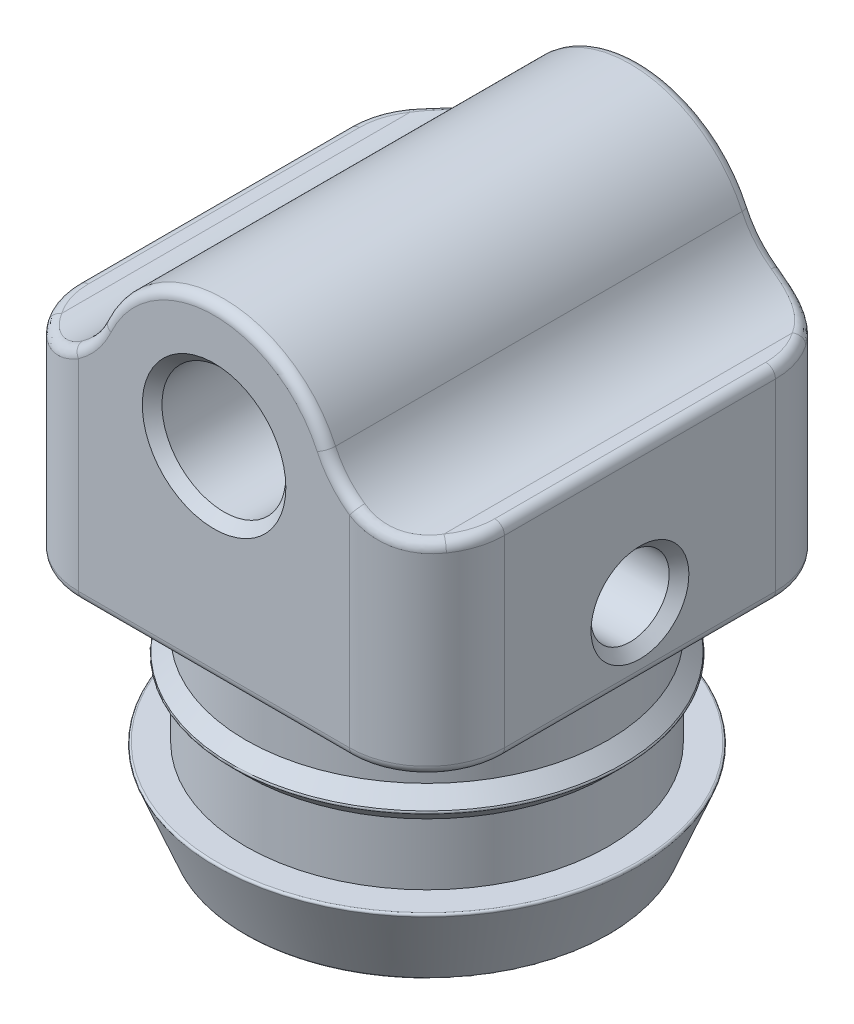
SolidWorks part; units mm, degrees
ref_plane "Front Plane" through (0, 0, 0) normal (0, 0, 1) x (1, 0, 0)
ref_plane "Top Plane" through (0, 0, 0) normal (0, 1, 0) x (1, 0, 0)
ref_plane "Right Plane" through (0, 0, 0) normal (1, 0, 0) x (0, 0, -1)
sketch "Sketch1" plane through (0, 0, 0) normal (0, 0, 1) x (1, 0, 0)
  line L3 (0, 0) -> (0, -10.5) construction
  line L4 (-11, 0) -> (-6.35, 0)
  line L5 (-11, 0) -> (-11, -10.5)
  line L6 (-11, -10.5) -> (11, -10.5)
  line L7 (11, 0) -> (11, -10.5)
  line L8 (6.35, 0) -> (11, 0)
  circle A0 centre (0, 0) radius 3.2
  arc A1 (6.35, 0) -> (-6.35, 0) centre (0, 0) ccw
  dimension "D1" = 6.4
  dimension "D2" = 12.7
  dimension "D4" = 22
  dimension "D5" = 10.5
extrude "Boss-Extrude1" add sketch "Sketch1" along normal mid plane 22
sketch3d "3DSketch1" plane through (0, 0, 0) normal (0, 0, 1) x (1, 0, 0)
  dimension "D1" = 12.7
sketch "Sketch2" plane through (0, 0, 0) normal (0, 0, 1) x (1, 0, 0)
  line L0 (0, 9.544) -> (0, -9.544) construction
  line L1 (0, -10) -> (9.365, -10)
  line L4 (0, -22.7) -> (9.365, -22.7)
  line L10 (0, -22.7) -> (0, -10)
  line L11 (9.365, -22.7) -> (10.9525, -18.7312)
  line L12 (10.9525, -18.7312) -> (9.365, -18.7312)
  line L13 (9.365, -18.7312) -> (9.365, -15.5562)
  line L14 (9.365, -15.5562) -> (10.1587, -14.7625)
  line L15 (10.1587, -14.7625) -> (9.365, -13.9687)
  line L16 (10.1587, -14.7625) -> (9.365, -14.7625) construction
  line L17 (9.365, -13.9687) -> (9.365, -10)
  dimension "D1" = 18.73
  dimension "D2" = 12.7
  dimension "D3" = 1.5875
  dimension "D4" = 3.9688
  dimension "D5" = 0.7937
  dimension "D6" = 7.9375
  dimension "D7" = 10
revolve "Revolve1" add sketch "Sketch2" angle 360 about L0
sketch "Sketch3" plane through (0, -22.7, 0) normal (0, -1, 0) x (1, 0, 0)
  circle A0 centre (0, 0) radius 2.3813
  dimension "D1" = 4.7625
extrude "Cut-Extrude1" cut sketch "Sketch3" against normal blind 18 contours A0
hole_wizard "#10-32 Tapped Hole1" positions "Sketch4" profile "Sketch5" tap size "#10-32" standard "ANSI Inch"
sketch "Sketch4" plane through (11, 0, 0) normal (1, 0, 0) x (0, 0, -1)
  point P0 (0, -7)
  dimension "D1" = 7
sketch "Sketch5" plane through (11, -7, 0) normal (0, 1, 0) x (0, 0, -1)
  line L0 (0, 0) -> (0, 8.6188)
  line L1 (0, 8.6188) -> (2.0193, 8.6188)
  line L2 (2.0193, 8.6188) -> (2.0193, 0)
  line L5 (2.0193, 0) -> (0, 0)
  line L11 (0, -6.35) -> (0, 107.95) construction
  dimension "Thru Tap Drill Dia." = 4.0386
  dimension "Thru Tap Drill Depth" = 8.6188
cosmetic thread "Hole Thread1" parameters "D2"=4.826
fillet "Fillet3" radius 0.0992 6 edges at (-10.9525, -18.7312, 0) (-10.1587, -14.7625, 0) (2.3813, -22.7, 0) (2.3813, -4.7, 0) (2.3577, -8.9915, -0.3339) (-9.365, -22.7, 0)
chamfer "Chamfer1" distance 0.508 angle 45 3 edges at (3.2, 0, -11) (3.2, 0, 11) (11, -7, -2.0193)
fillet "Fillet7" radius 4.5 2 edges at (-6.35, 0, 0) (6.35, 0, 0)
fillet "Fillet6" radius 4 4 edges at (11, -5.25, -11) (-11, -5.25, -11) (-11, -5.25, 11) (11, -5.25, 11)
fillet "Fillet8" radius 0.5 24 edges at (-9.8284, -10.5, 9.8284) (-11, -10.5, 0) (-9.8284, -10.5, -9.8284) (0, -10.5, -11) (9.8284, -10.5, -9.8284) (11, -10.5, 0) (9.8284, -10.5, 9.8284) (10.7075, 0, 8.5015) (8.9278, 0.1004, 10.5048) (6.2987, 1.7659, 11) (0, 6.35, 11) (-6.2987, 1.7659, 11) (-8.0042, 0.4063, 10.8719) (-10.7075, 0, 8.5015) (-11, 0, 0) (-10.7075, 0, -8.5015) (-8.9278, 0.1004, -10.5048) (-6.2987, 1.7659, -11) (0, 6.35, -11) (6.2987, 1.7659, -11) (8.0042, 0.4063, -10.8719) (10.7075, 0, -8.5015) (0, -10.5, 11) (11, 0, 0)
